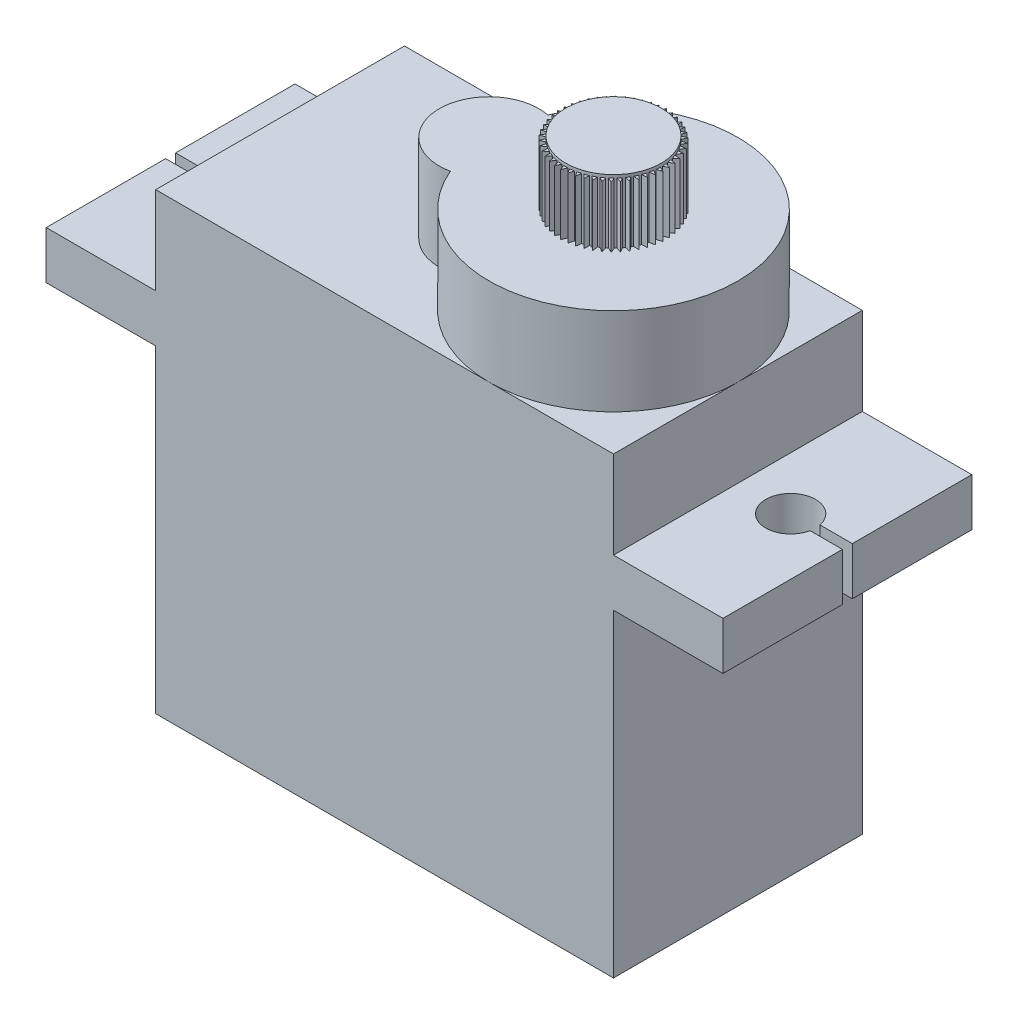
SolidWorks part; units mm, degrees
ref_plane "Front Plane" through (0, 0, 0) normal (0, 0, 1) x (1, 0, 0)
ref_plane "Top Plane" through (0, 0, 0) normal (0, 1, 0) x (1, 0, 0)
ref_plane "Right Plane" through (0, 0, 0) normal (1, 0, 0) x (0, 0, -1)
sketch "Sketch2" plane through (0, 0, 0) normal (0, 1, 0) x (1, 0, 0)
  line L1 (-11.5, -6.25) -> (11.5, -6.25)
  line L2 (-11.5, -6.25) -> (-11.5, 6.25)
  line L3 (-11.5, 6.25) -> (11.5, 6.25)
  line L4 (11.5, -6.25) -> (11.5, 6.25)
  line L5 (-11.5, -6.25) -> (11.5, 6.25) construction
  line L6 (-11.5, 6.25) -> (11.5, -6.25) construction
  point P0 (0, 0)
  dimension "D1" = 12.5
  dimension "D2" = 23
extrude "Boss-Extrude1" add sketch "Sketch2" along normal blind 16
sketch "Sketch3" plane through (0, 16, 0) normal (0, 1, 0) x (1, 0, 0)
  line L0 (0, 0) -> (0, 10.1004) construction
  line L1 (-11.5, 6.25) -> (-17, 6.25)
  line L3 (-11.5, -6.25) -> (-17, -6.25)
  line L4 (-17, 6.25) -> (-17, -6.25)
  line L5 (17, 6.25) -> (17, -6.25)
  line L6 (11.5, -6.25) -> (17, -6.25)
  line L8 (11.5, 6.25) -> (17, 6.25)
  line L9 (-11.5, -6.25) -> (11.5, -6.25) construction
  line L10 (11.5, 6.25) -> (-11.5, 6.25) construction
  line L11 (-11.5, -6.25) -> (11.5, -6.25)
  line L12 (11.5, 6.25) -> (-11.5, 6.25)
  dimension "D1" = 5.5
extrude "Boss-Extrude2" add sketch "Sketch3" along normal blind 2.4
sketch "Sketch4" plane through (0, 18.4, 0) normal (0, 1, 0) x (1, 0, 0)
  line L4 (-11.5, -6.25) -> (11.5, -6.25)
  line L5 (11.5, -6.25) -> (11.5, 6.25)
  line L6 (11.5, 6.25) -> (-11.5, 6.25)
  line L7 (-11.5, 6.25) -> (-11.5, -6.25)
  line L8 (-11.5, -6.25) -> (11.5, -6.25)
  line L9 (11.5, -6.25) -> (11.5, 6.25)
  line L10 (11.5, 6.25) -> (-11.5, 6.25)
  line L11 (-11.5, 6.25) -> (-11.5, -6.25)
  dimension "D1" = 0
extrude "Boss-Extrude3" add sketch "Sketch4" along normal blind 4.4
sketch "Sketch5" plane through (0, 18.4, 0) normal (0, 1, 0) x (1, 0, 0)
  line L0 (-11.5, 6.25) -> (-11.5, -6.25) construction
  circle A0 centre (-14.15, 0) radius 1.25
  dimension "D1" = 2.65
  dimension "D2" = 2.5
extrude "Cut-Extrude1" cut sketch "Sketch5" against normal blind 4.4
mirror "Mirror1" about plane through (0, 0, 0) normal (1, 0, 0) of "Cut-Extrude1"
sketch "Sketch6" plane through (0, 18.4, 0) normal (0, 1, 0) x (1, 0, 0)
  line L1 (-13.4759, -0.25) -> (-17.3241, -0.25)
  line L2 (-13.4759, -0.25) -> (-13.4759, 0.25)
  line L3 (-13.4759, 0.25) -> (-17.3241, 0.25)
  line L4 (-17.3241, -0.25) -> (-17.3241, 0.25)
  line L5 (-13.4759, -0.25) -> (-17.3241, 0.25) construction
  line L6 (-13.4759, 0.25) -> (-17.3241, -0.25) construction
  circle A0 centre (-14.15, 0) radius 1.25 construction
  point P0 (-15.4, 0)
  dimension "D1" = 0.5
extrude "Cut-Extrude2" cut sketch "Sketch6" against normal blind 4.4
mirror "Mirror2" about plane through (0, 0, 0) normal (1, 0, 0) of "Cut-Extrude2"
sketch "Sketch7" plane through (0, 22.8, 0) normal (0, 1, 0) x (1, 0, 0)
  line L0 (11.5, -6.25) -> (11.5, 6.25) construction
  circle A0 centre (5.25, 0) radius 6.25
extrude "Boss-Extrude4" add sketch "Sketch7" along normal blind 4.4
sketch "Sketch8" plane through (0, 22.8, 0) normal (0, 1, 0) x (1, 0, 0)
  circle A0 centre (-1, 0) radius 2.5
  arc A1 (5.25, 6.25) -> (5.25, -6.25) centre (5.25, 0) ccw construction
  dimension "D1" = 5
extrude "Boss-Extrude5" add sketch "Sketch8" along normal blind 4.4
sketch "Sketch9" plane through (0, 27.2, 0) normal (0, 1, 0) x (1, 0, 0)
  circle A0 centre (5.25, 0) radius 2.4
  dimension "D1" = 4.8
extrude "Boss-Extrude6" add sketch "Sketch9" along normal blind 3.2
sketch "Sketch10" plane through (0, 27.2, 0) normal (0, 1, 0) x (1, 0, 0)
  line L0 (5.25, 0) -> (5.25, 4.0724) construction
  line L1 (5.35, 2.3979) -> (5.25, 2.6516)
  line L2 (5.15, 2.3979) -> (5.25, 2.6516)
  line L3 (5.15, 2.3979) -> (5.25, 2.2979)
  line L4 (5.25, 2.2979) -> (5.35, 2.3979)
  circle A0 centre (5.25, 0) radius 2.4 construction
  dimension "D1" = 0.1
extrude "Boss-Extrude7" add sketch "Sketch10" along normal blind 3.05
pattern_circular "CirPattern1" count 50 over 360 about axis through (5.25, 0, 0) along (0, 1, 0) of "Boss-Extrude7"
